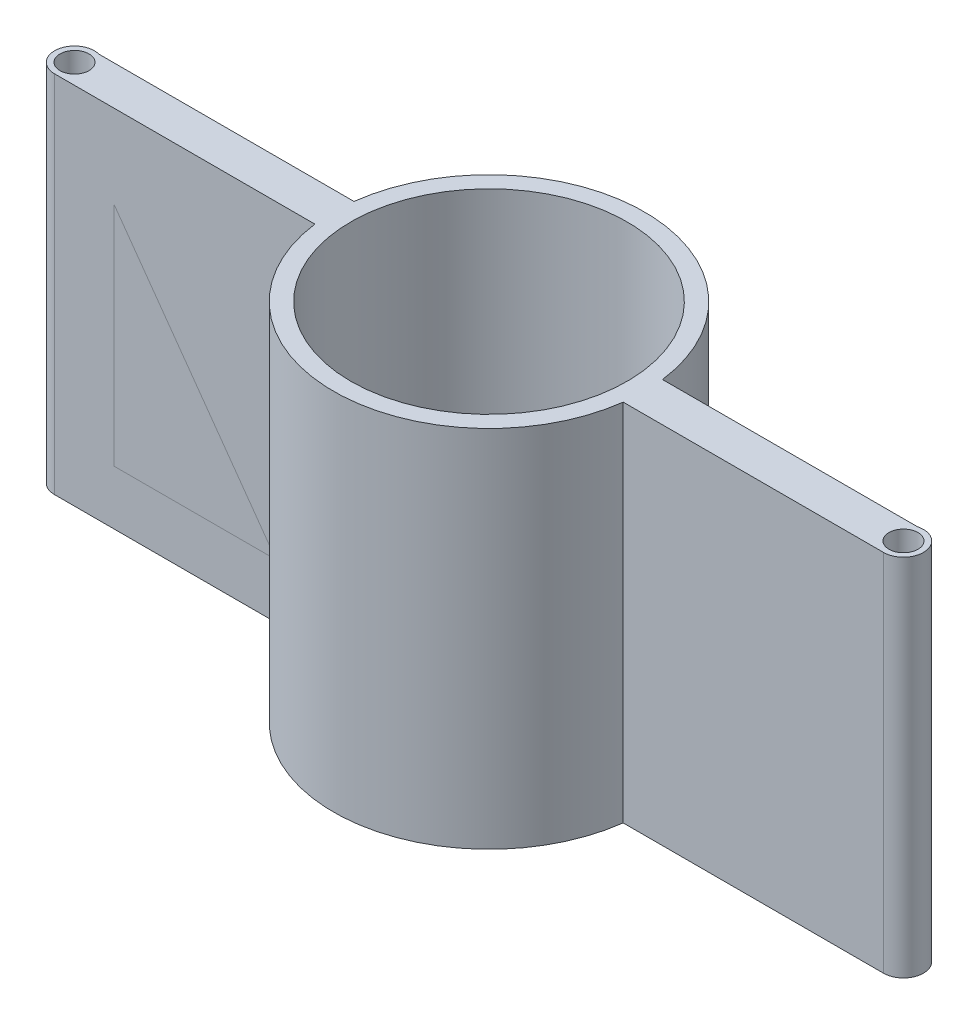
SolidWorks part; units mm, degrees
other "COLL.BOX-Boss-Extrude3"
other "COLL.BOX-Boss-Extrude2"
ref_plane "Front Plane" through (0, 0, 0) normal (0, 0, 1) x (1, 0, 0)
ref_plane "Top Plane" through (0, 0, 0) normal (0, 1, 0) x (1, 0, 0)
ref_plane "Right Plane" through (0, 0, 0) normal (1, 0, 0) x (0, 0, -1)
sketch "Sketch1" plane through (0, 0, 0) normal (0, 1, 0) x (1, 0, 0)
  line L0 (-76.2, -3.6691) -> (25.2594, -3.6691)
  line L1 (25.2727, 2.5399) -> (-76.2, 2.5399)
  line L2 (-76.2, -2.6691) -> (25.2594, -2.6691)
  line L3 (0, -2.6691) -> (0, 2.54)
  line L4 (25.2727, 3.5399) -> (-76.2, 3.5399)
  line L5 (0, -28.575) -> (0, 28.575)
  line L6 (-25.2727, 3.5399) -> (76.2, 3.5399)
  line L7 (76.2, -2.6691) -> (-25.2594, -2.6691)
  line L8 (-25.2727, 2.5399) -> (76.2, 2.5399)
  line L9 (76.2, -3.6691) -> (-25.2594, -3.6691)
  circle A0 centre (0, 0) radius 25.4
  circle A1 centre (0, 0) radius 28.575
  circle A2 centre (-76.2, 0) radius 0.1291
  circle A3 centre (-76.2, 0) radius 2.6691
  circle A4 centre (-76.2, 0) radius 3.6691
  circle A5 centre (76.2, 0) radius 3.6691
  circle A6 centre (76.2, 0) radius 2.6691
  circle A7 centre (76.2, 0) radius 0.1291
  dimension "D1" = 50.8
  dimension "D2" = 57.15
  dimension "D3" = 5.209
  dimension "D4" = 2.54
  dimension "D5" = 1
extrude "Boss-Extrude1" add sketch "Sketch1" along normal blind 67
sketch "Sketch2" plane through (0, 67, 0) normal (0, 1, 0) x (1, 0, 0)
  line L0 (76.2, -3.6691) -> (28.3385, -3.6691) construction
  line L1 (28.3549, 3.5399) -> (69.2, 3.5399)
  line L2 (28.3549, 3.5399) -> (28.3549, -3.6691)
  line L3 (28.3549, -3.6691) -> (69.2, -3.6691)
  line L4 (69.2, 3.5399) -> (69.2, -3.6691)
  circle A0 centre (76.2, 0) radius 2.6691 construction
  dimension "D1" = 7
sketch "Sketch3" plane through (0, 67, 0) normal (0, 1, 0) x (1, 0, 0)
  line L0 (-76.2, -3.6691) -> (-28.3385, -3.6691) construction
  line L1 (-28.3549, 3.5399) -> (-69.2, 3.5399)
  line L2 (-28.3549, 3.5399) -> (-28.3549, -3.6691)
  line L3 (-28.3549, -3.6691) -> (-69.2, -3.6691)
  line L4 (-69.2, 3.5399) -> (-69.2, -3.6691)
  circle A0 centre (-76.2, 0) radius 2.6691 construction
  dimension "D1" = 7
sketch "Sketch4" plane through (0, 0, -3.5399) normal (0, 0, -1) x (-1, 0, 0)
  line L0 (28.3549, 67) -> (28.3549, 0) construction
  line L1 (28.3549, 57) -> (65.2346, 57)
  line L2 (28.3549, 57) -> (28.3549, 10)
  line L3 (28.3549, 10) -> (65.2346, 10)
  line L4 (65.2346, 57) -> (65.2346, 10)
  line L5 (28.3549, 67) -> (69.2, 67) construction
  line L6 (28.3549, 0) -> (75.2346, 0) construction
  line L9 (75.2346, 67) -> (75.2346, 0) construction
  dimension "D1" = 10
  dimension "D2" = 10
  dimension "D3" = 10
extrude "Boss-Extrude2" add sketch "Sketch4" against normal up to surface (7.209 mm away) separate body up to face at (-52.2692, 33.5, 3.6691)
sketch "Sketch5" plane through (0, 0, -3.5399) normal (0, 0, -1) x (-1, 0, 0)
  line L0 (-28.3549, 67) -> (-28.3549, 0) construction
  line L1 (-28.3549, 57) -> (-65.2346, 57)
  line L2 (-28.3549, 57) -> (-28.3549, 10)
  line L3 (-28.3549, 10) -> (-65.2346, 10)
  line L4 (-65.2346, 57) -> (-65.2346, 10)
  line L5 (-75.2346, 67) -> (-75.2346, 0) construction
  line L6 (-28.3549, 67) -> (-69.2, 67) construction
  line L7 (-28.3549, 0) -> (-75.2346, 0) construction
  dimension "D1" = 10
  dimension "D2" = 10
  dimension "D3" = 10
extrude "Boss-Extrude3" add sketch "Sketch5" against normal up to surface (7.209 mm away) separate body up to face at (52.2692, 33.5, 3.6691)
